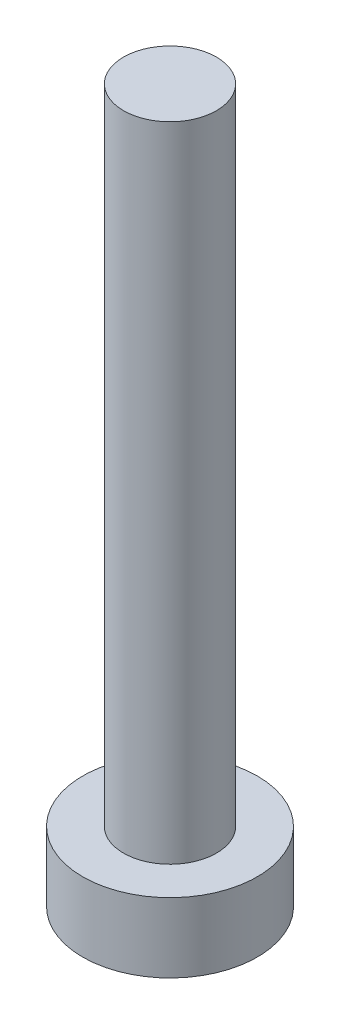
SolidWorks part; units mm, degrees
ref_plane "Front Plane" through (0, 0, 0) normal (0, 0, 1) x (1, 0, 0)
ref_plane "Top Plane" through (0, 0, 0) normal (0, 1, 0) x (1, 0, 0)
ref_plane "Right Plane" through (0, 0, 0) normal (1, 0, 0) x (0, 0, -1)
sketch "Sketch1" plane through (0, 0, 0) normal (0, 1, 0) x (1, 0, 0)
  circle A0 centre (0, 0) radius 1.335
extrude "Boss-Extrude1" add sketch "Sketch1" along normal blind 18.48
sketch "Sketch2" plane through (0, 0, 0) normal (0, -1, 0) x (1, 0, 0)
  circle A0 centre (0, 0) radius 2.51
extrude "Boss-Extrude2" add sketch "Sketch2" along normal blind 2
